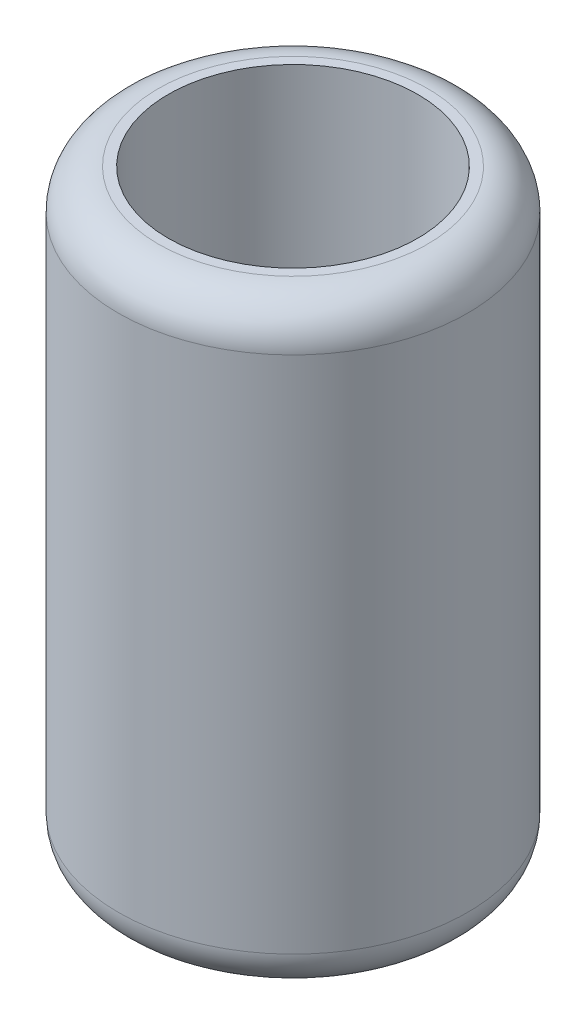
SolidWorks part; units mm, degrees
ref_plane "Front Plane" through (0, 0, 0) normal (0, 0, 1) x (1, 0, 0)
ref_plane "Top Plane" through (0, 0, 0) normal (0, 1, 0) x (1, 0, 0)
ref_plane "Right Plane" through (0, 0, 0) normal (1, 0, 0) x (0, 0, -1)
sketch "Sketch1" plane through (0, 0, 0) normal (0, 1, 0) x (1, 0, 0)
  circle A0 centre (0, 0) radius 11.1125
  dimension "D1" = 22.225
extrude "Boss-Extrude1" add sketch "Sketch1" along normal blind 38.1
sketch "Sketch2" plane through (0, 38.1, 0) normal (0, 1, 0) x (1, 0, 0)
  circle A0 centre (0, 0) radius 7.9375
  dimension "D1" = 15.875
extrude "Cut-Extrude1" cut sketch "Sketch2" against normal through all
fillet "Fillet2" radius 2.54 2 edges at (0, 0, 11.1125) (0, 38.1, 11.1125)
